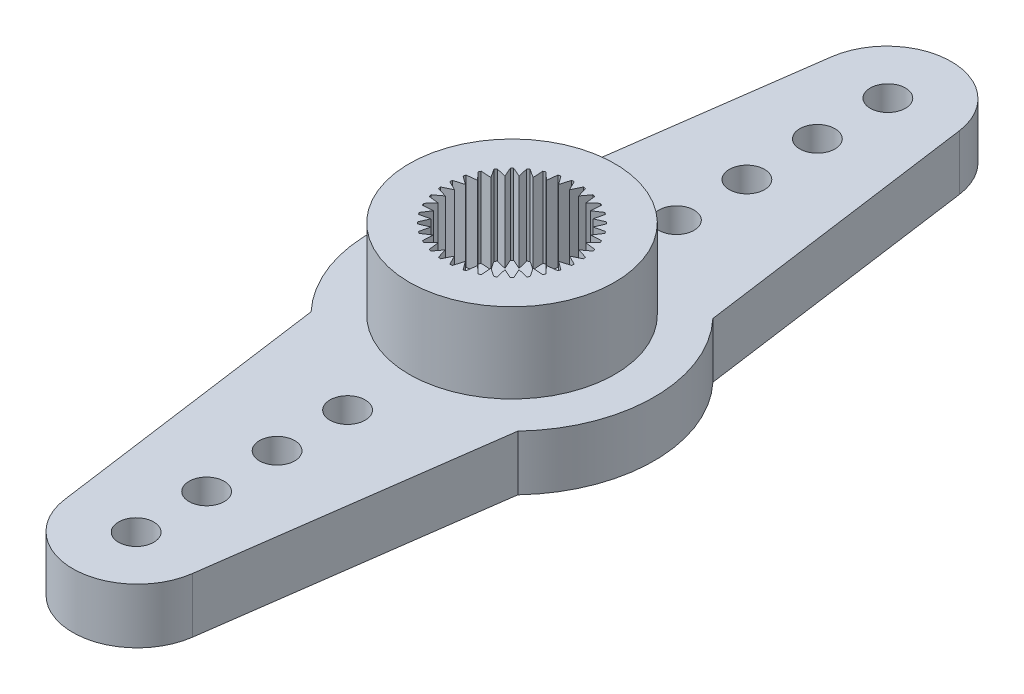
SolidWorks part; units mm, degrees
ref_plane "Front Plane" through (0, 0, 0) normal (0, 0, 1) x (1, 0, 0)
ref_plane "Top Plane" through (0, 0, 0) normal (0, 1, 0) x (1, 0, 0)
ref_plane "Right Plane" through (0, 0, 0) normal (1, 0, 0) x (0, 0, -1)
ref_plane "Plane1" through (0, 2.35, 0) normal (0, 1, 0) x (1, 0, 0)
sketch "Sketch1" plane through (0, 2.35, 0) normal (0, 1, 0) x (1, 0, 0)
  line L0 (2.7243, -16.325) -> (4.4, -4.1524)
  line L1 (4.4, 4.1524) -> (2.7243, 16.325)
  line L2 (-2.7243, 16.325) -> (-4.4, 4.1524)
  line L3 (-4.4, -4.1524) -> (-2.7243, -16.325)
  arc A0 (-2.7243, -16.325) -> (2.7243, -16.325) centre (0, -15.95) ccw
  arc A1 (4.4, -4.1524) -> (4.4, 4.1524) centre (0, 0) ccw
  arc A2 (2.7243, 16.325) -> (-2.7243, 16.325) centre (0, 15.95) ccw
  arc A3 (-4.4, 4.1524) -> (-4.4, -4.1524) centre (0, 0) ccw
extrude "Boss-Extrude1" add sketch "Sketch1" against normal blind 2.35
sketch "Sketch2" plane through (0, 2.35, 0) normal (0, 1, 0) x (-1, 0, 0)
  circle A0 centre (0, 0) radius 4.375
extrude "Boss-Extrude2" add sketch "Sketch2" along normal blind 3.4
sketch "Sketch3" plane through (0, 5.75, 0) normal (0, 1, 0) x (-1, 0, 0)
  line L0 (0.6873, 2.7659) -> (0.4254, 2.4128)
  line L1 (0.4254, 2.4128) -> (0.3001, 2.8342)
  line L2 (0.1966, 2.8432) -> (0, 2.45)
  line L3 (0, 2.45) -> (-0.1966, 2.8432)
  line L4 (-0.3001, 2.8342) -> (-0.4254, 2.4128)
  line L5 (-0.4254, 2.4128) -> (-0.6873, 2.7659)
  line L6 (-0.7877, 2.739) -> (-0.8379, 2.3022)
  line L7 (-0.8379, 2.3022) -> (-1.1572, 2.6045)
  line L8 (-1.2513, 2.5606) -> (-1.225, 2.1218)
  line L9 (-1.225, 2.1218) -> (-1.5919, 2.364)
  line L10 (-1.677, 2.3044) -> (-1.5748, 1.8768)
  line L11 (-1.5748, 1.8768) -> (-1.9782, 2.0517)
  line L12 (-2.0517, 1.9782) -> (-1.8768, 1.5748)
  line L13 (-1.8768, 1.5748) -> (-2.3044, 1.677)
  line L14 (-2.364, 1.5919) -> (-2.1218, 1.225)
  line L15 (-2.1218, 1.225) -> (-2.5606, 1.2513)
  line L16 (-2.6045, 1.1572) -> (-2.3022, 0.8379)
  line L17 (-2.3022, 0.8379) -> (-2.739, 0.7877)
  line L18 (-2.7659, 0.6873) -> (-2.4128, 0.4254)
  line L19 (-2.4128, 0.4254) -> (-2.8342, 0.3001)
  line L20 (-2.8432, 0.1966) -> (-2.45, 0)
  line L21 (-2.45, 0) -> (-2.8432, -0.1966)
  line L22 (-2.8342, -0.3001) -> (-2.4128, -0.4254)
  line L23 (-2.4128, -0.4254) -> (-2.7659, -0.6873)
  line L24 (-2.739, -0.7877) -> (-2.3022, -0.8379)
  line L25 (-2.3022, -0.8379) -> (-2.6045, -1.1572)
  line L26 (-2.5606, -1.2513) -> (-2.1218, -1.225)
  line L27 (-2.1218, -1.225) -> (-2.364, -1.5919)
  line L28 (-2.3044, -1.677) -> (-1.8768, -1.5748)
  line L29 (-1.8768, -1.5748) -> (-2.0517, -1.9782)
  line L30 (-1.9782, -2.0517) -> (-1.5748, -1.8768)
  line L31 (-1.5748, -1.8768) -> (-1.677, -2.3044)
  line L32 (-1.5919, -2.364) -> (-1.225, -2.1218)
  line L33 (-1.225, -2.1218) -> (-1.2513, -2.5606)
  line L34 (-1.1572, -2.6045) -> (-0.8379, -2.3022)
  line L35 (-0.8379, -2.3022) -> (-0.7877, -2.739)
  line L36 (-0.6873, -2.7659) -> (-0.4254, -2.4128)
  line L37 (-0.4254, -2.4128) -> (-0.3001, -2.8342)
  line L38 (-0.1966, -2.8432) -> (0, -2.45)
  line L39 (0, -2.45) -> (0.1966, -2.8432)
  line L40 (0.3001, -2.8342) -> (0.4254, -2.4128)
  line L41 (0.4254, -2.4128) -> (0.6873, -2.7659)
  line L42 (0.7877, -2.739) -> (0.8379, -2.3022)
  line L43 (0.8379, -2.3022) -> (1.1572, -2.6045)
  line L44 (1.2513, -2.5606) -> (1.225, -2.1218)
  line L45 (1.225, -2.1218) -> (1.5919, -2.364)
  line L46 (1.677, -2.3044) -> (1.5748, -1.8768)
  line L47 (1.5748, -1.8768) -> (1.9782, -2.0517)
  line L48 (2.0517, -1.9782) -> (1.8768, -1.5748)
  line L49 (1.8768, -1.5748) -> (2.3044, -1.677)
  line L50 (2.364, -1.5919) -> (2.1218, -1.225)
  line L51 (2.1218, -1.225) -> (2.5606, -1.2513)
  line L52 (2.6045, -1.1572) -> (2.3022, -0.8379)
  line L53 (2.3022, -0.8379) -> (2.739, -0.7877)
  line L54 (2.7659, -0.6873) -> (2.4128, -0.4254)
  line L55 (2.4128, -0.4254) -> (2.8342, -0.3001)
  line L56 (2.8432, -0.1966) -> (2.45, 0)
  line L57 (2.45, 0) -> (2.8432, 0.1966)
  line L58 (2.8342, 0.3001) -> (2.4128, 0.4254)
  line L59 (2.4128, 0.4254) -> (2.7659, 0.6873)
  line L60 (2.739, 0.7877) -> (2.3022, 0.8379)
  line L61 (2.3022, 0.8379) -> (2.6045, 1.1572)
  line L62 (2.5606, 1.2513) -> (2.1218, 1.225)
  line L63 (2.1218, 1.225) -> (2.364, 1.5919)
  line L64 (2.3044, 1.677) -> (1.8768, 1.5748)
  line L65 (1.8768, 1.5748) -> (2.0517, 1.9782)
  line L66 (1.9782, 2.0517) -> (1.5748, 1.8768)
  line L67 (1.5748, 1.8768) -> (1.677, 2.3044)
  line L68 (1.5919, 2.364) -> (1.225, 2.1218)
  line L69 (1.225, 2.1218) -> (1.2513, 2.5606)
  line L70 (1.1572, 2.6045) -> (0.8379, 2.3022)
  line L71 (0.8379, 2.3022) -> (0.7877, 2.739)
  arc A0 (0.3001, 2.8342) -> (0.1966, 2.8432) centre (0, 0) ccw
  arc A1 (-0.1966, 2.8432) -> (-0.3001, 2.8342) centre (0, 0) ccw
  arc A2 (-0.6873, 2.7659) -> (-0.7877, 2.739) centre (0, 0) ccw
  arc A3 (-1.1572, 2.6045) -> (-1.2513, 2.5606) centre (0, 0) ccw
  arc A4 (-1.5919, 2.364) -> (-1.677, 2.3044) centre (0, 0) ccw
  arc A5 (-1.9782, 2.0517) -> (-2.0517, 1.9782) centre (0, 0) ccw
  arc A6 (-2.3044, 1.677) -> (-2.364, 1.5919) centre (0, 0) ccw
  arc A7 (-2.5606, 1.2513) -> (-2.6045, 1.1572) centre (0, 0) ccw
  arc A8 (-2.739, 0.7877) -> (-2.7659, 0.6873) centre (0, 0) ccw
  arc A9 (-2.8342, 0.3001) -> (-2.8432, 0.1966) centre (0, 0) ccw
  arc A10 (-2.8432, -0.1966) -> (-2.8342, -0.3001) centre (0, 0) ccw
  arc A11 (-2.7659, -0.6873) -> (-2.739, -0.7877) centre (0, 0) ccw
  arc A12 (-2.6045, -1.1572) -> (-2.5606, -1.2513) centre (0, 0) ccw
  arc A13 (-2.364, -1.5919) -> (-2.3044, -1.677) centre (0, 0) ccw
  arc A14 (-2.0517, -1.9782) -> (-1.9782, -2.0517) centre (0, 0) ccw
  arc A15 (-1.677, -2.3044) -> (-1.5919, -2.364) centre (0, 0) ccw
  arc A16 (-1.2513, -2.5606) -> (-1.1572, -2.6045) centre (0, 0) ccw
  arc A17 (-0.7877, -2.739) -> (-0.6873, -2.7659) centre (0, 0) ccw
  arc A18 (-0.3001, -2.8342) -> (-0.1966, -2.8432) centre (0, 0) ccw
  arc A19 (0.1966, -2.8432) -> (0.3001, -2.8342) centre (0, 0) ccw
  arc A20 (0.6873, -2.7659) -> (0.7877, -2.739) centre (0, 0) ccw
  arc A21 (1.1572, -2.6045) -> (1.2513, -2.5606) centre (0, 0) ccw
  arc A22 (1.5919, -2.364) -> (1.677, -2.3044) centre (0, 0) ccw
  arc A23 (1.9782, -2.0517) -> (2.0517, -1.9782) centre (0, 0) ccw
  arc A24 (2.3044, -1.677) -> (2.364, -1.5919) centre (0, 0) ccw
  arc A25 (2.5606, -1.2513) -> (2.6045, -1.1572) centre (0, 0) ccw
  arc A26 (2.739, -0.7877) -> (2.7659, -0.6873) centre (0, 0) ccw
  arc A27 (2.8342, -0.3001) -> (2.8432, -0.1966) centre (0, 0) ccw
  arc A28 (2.8432, 0.1966) -> (2.8342, 0.3001) centre (0, 0) ccw
  arc A29 (2.7659, 0.6873) -> (2.739, 0.7877) centre (0, 0) ccw
  arc A30 (2.6045, 1.1572) -> (2.5606, 1.2513) centre (0, 0) ccw
  arc A31 (2.364, 1.5919) -> (2.3044, 1.677) centre (0, 0) ccw
  arc A32 (2.0517, 1.9782) -> (1.9782, 2.0517) centre (0, 0) ccw
  arc A33 (1.677, 2.3044) -> (1.5919, 2.364) centre (0, 0) ccw
  arc A34 (1.2513, 2.5606) -> (1.1572, 2.6045) centre (0, 0) ccw
  arc A35 (0.7877, 2.739) -> (0.6873, 2.7659) centre (0, 0) ccw
extrude "Cut-Extrude1" cut sketch "Sketch3" against normal blind 3.4
hole_wizard "Hole1" positions "Sketch5" profile "Sketch4" legacy
sketch "Sketch5" plane through (0, 0, 0) normal (0, -1, 0) x (-1, 0, 0)
  point P0 (0, 0)
sketch "Sketch4" plane through (0, 0, 0) normal (1, 0, 0) x (0, 0, -1)
  line L0 (0, 0) -> (0, 0.3)
  line L1 (0, 0.3) -> (4.4, 0.3)
  line L2 (4.4, 0.3) -> (4.4, 0)
  line L3 (4.4, 0) -> (0, 0)
  line L4 (0, 110) -> (0, -10) construction
  dimension "Diameter" = 8.8
  dimension "Depth" = 0.3
sketch "Sketch6" plane through (0, 0, 0) normal (0, 0, 1) x (1, 0, 0)
  line L0 (3.25, 0.3) -> (0, 0.3)
  line L1 (0, 0.3) -> (0, 0)
  line L2 (0, 0) -> (3.25, 0)
  line L3 (3.25, 0) -> (3.25, 0.3)
  line L4 (0, 0.3) -> (0, 0) construction
revolve "Revolve1" add sketch "Sketch6" angle 360 about L4
hole_wizard "#00 Clearance Hole1" positions "Sketch8" profile "Sketch7" hole size "#00" standard "ANSI Inch"
sketch "Sketch8" plane through (0, 2.35, 0) normal (0, 1, 0) x (1, 0, 0)
  point P0 (0, -7)
  point P1 (0, 16)
  point P2 (0, -10)
  point P3 (0, -13)
  point P4 (0, -16)
  point P5 (0, 13)
  point P6 (0, 10)
  point P7 (0, 7)
sketch "Sketch7" plane through (0, 2.35, 7) normal (1, 0, 0) x (0, 0, 1)
  line L0 (0, 0) -> (0, 2.35)
  line L1 (0, 2.35) -> (0.75, 2.35)
  line L2 (0.75, 2.35) -> (0.75, 0)
  line L5 (0.75, 0) -> (0, 0)
  line L11 (0, -6.35) -> (0, 107.95) construction
  dimension "Thru Hole Dia." = 1.5
  dimension "Thru Hole Depth" = 2.35
hole_wizard "CBORE for #3 Binding Head Machine Screw1" positions "Sketch10" profile "Sketch9" counterbore size "#3" standard "ANSI Inch"
sketch "Sketch10" plane through (0, 0, 0) normal (0, -1, 0) x (-1, 0, 0)
  point P0 (0, 0)
sketch "Sketch9" plane through (0, 0, 0) normal (1, 0, 0) x (0, 0, -1)
  line L0 (0, 0) -> (0, 5.75)
  line L1 (0, 5.75) -> (1.5, 5.75)
  line L3 (1.5, 5.75) -> (1.5, 0.3)
  line L4 (1.5, 0.3) -> (2.75, 0.3)
  line L5 (2.75, 0.3) -> (2.75, 0)
  line L7 (2.75, 0) -> (0, 0)
  line L11 (0, -6.35) -> (0, 107.95) construction
  dimension "Thru Hole Dia." = 3
  dimension "Thru Hole Depth" = 5.75
  dimension "C'Bore Dia." = 5.5
  dimension "C'Bore Depth" = 0.3
